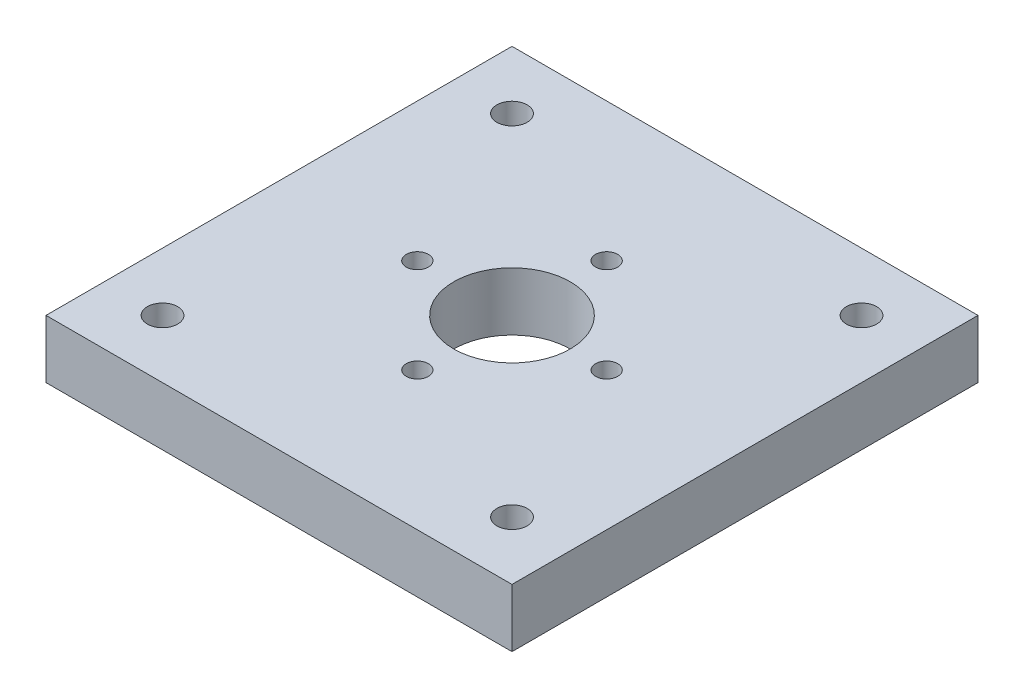
SolidWorks part; units mm, degrees
ref_plane "Front Plane" through (0, 0, 0) normal (0, 0, 1) x (1, 0, 0)
ref_plane "Top Plane" through (0, 0, 0) normal (0, 1, 0) x (1, 0, 0)
ref_plane "Right Plane" through (0, 0, 0) normal (1, 0, 0) x (0, 0, -1)
sketch "Sketch1" plane through (0, 0, 0) normal (0, 1, 0) x (1, 0, 0)
  line L1 (-2, 2) -> (2, 2)
  line L2 (-2, 2) -> (-2, -2)
  line L3 (-2, -2) -> (2, -2)
  line L4 (2, 2) -> (2, -2)
  line L5 (0, -2) -> (0, 2) construction
  line L6 (-2, 0) -> (2, 0) construction
  circle A0 centre (0, 0) radius 0.5
  circle A1 centre (0, 0) radius 0.8125 construction
  circle A2 centre (0, 0.8125) radius 0.095
  circle A3 centre (0.8125, 0) radius 0.095
  circle A4 centre (0, -0.8125) radius 0.095
  circle A5 centre (-0.8125, 0) radius 0.095
  circle A6 centre (-1.5, 1.5) radius 0.13
  circle A7 centre (1.5, 1.5) radius 0.13
  circle A8 centre (-1.5, -1.5) radius 0.13
  circle A9 centre (1.5, -1.5) radius 0.13
  point P0 (0, 0)
  point P21 (0, 0)
  point P27 (0, 0)
  point P28 (0, 0)
  point P29 (0, 0)
  point P30 (0, 0)
  point P31 (0, 0)
  dimension "D3" = 1
  dimension "D4" = 1.625
  dimension "D5" = 0.19
  dimension "D7" = 0.5
  dimension "D11" = 0.26
  dimension "D1" = 4
  dimension "D2" = 4
  dimension "D8" = 0.5
  dimension "D9" = 3
  dimension "D10" = 3
  dimension "D6" = 4
extrude "Boss-Extrude1" add sketch "Sketch1" along normal blind 0.5
